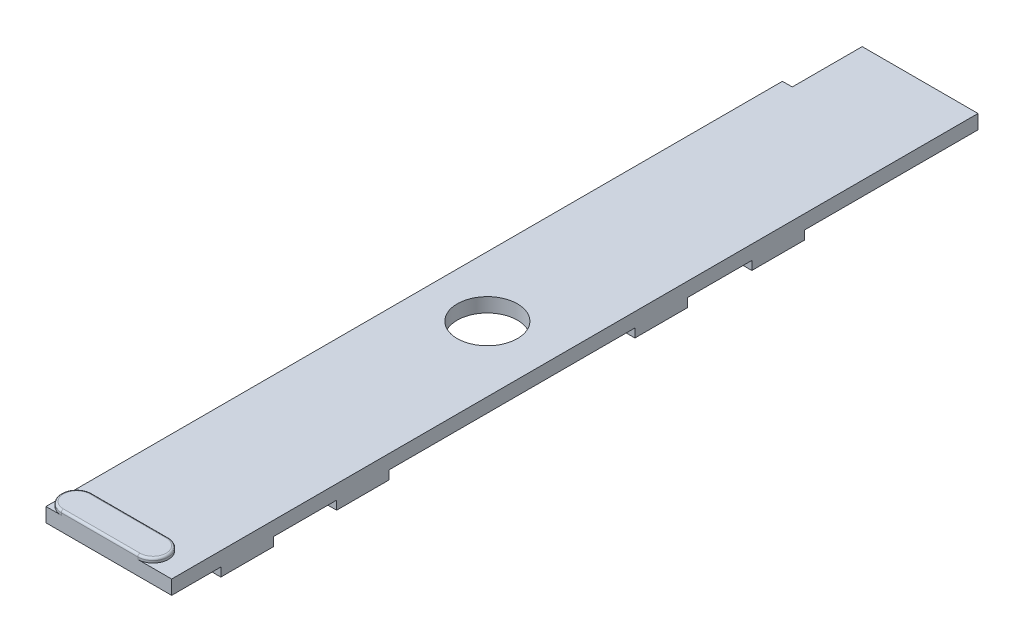
SolidWorks part; units mm, degrees
ref_plane "Front Plane" through (0, 0, 0) normal (0, 0, 1) x (1, 0, 0)
ref_plane "Top Plane" through (0, 0, 0) normal (0, 1, 0) x (1, 0, 0)
ref_plane "Right Plane" through (0, 0, 0) normal (1, 0, 0) x (0, 0, -1)
sketch "Sketch1" plane through (0, 0, 0) normal (0, 1, 0) x (1, 0, 0)
  line L1 (0, 0) -> (14.605, 0)
  line L2 (0, 0) -> (0, 93.726)
  line L3 (0, 93.726) -> (14.605, 93.726)
  line L4 (14.605, 0) -> (14.605, 93.726)
  line L5 (0, 93.726) -> (1.143, 93.726)
  line L6 (0, 93.726) -> (0, 85.598)
  line L7 (0, 85.598) -> (1.143, 85.598)
  line L8 (1.143, 93.726) -> (1.143, 85.598)
  circle A0 centre (7, 44.3) radius 3.5
  dimension "D1" = 14.605
  dimension "D5" = 7
  dimension "D2" = 93.726
  dimension "D3" = 8.128
  dimension "D4" = 1.143
  dimension "D6" = 7
  dimension "D7" = 44.3
extrude "Boss-Extrude1" add sketch "Sketch1" along normal blind 1.651 contours L3 L8 L7 L2 L1 L4 A0
sketch "Sketch2" plane through (0, 1.651, 0) normal (0, 1, 0) x (1, 0, 0)
  line L0 (1.778, 1.778) -> (10.668, 1.778) construction
  line L1 (1.778, 3.556) -> (10.668, 3.556)
  line L2 (1.778, 0) -> (10.668, 0)
  line L10 (14.605, 93.726) -> (1.143, 93.726)
  line L11 (1.143, 93.726) -> (1.143, 85.598)
  line L12 (1.143, 85.598) -> (0, 85.598)
  line L13 (0, 85.598) -> (0, 0)
  line L14 (0, 0) -> (14.605, 0)
  line L15 (14.605, 0) -> (14.605, 93.726)
  line L16 (14.605, 93.726) -> (1.143, 93.726)
  line L17 (1.143, 93.726) -> (1.143, 85.598)
  line L18 (1.143, 85.598) -> (0, 85.598)
  line L19 (0, 85.598) -> (0, 0)
  line L20 (0, 0) -> (14.605, 0)
  line L21 (14.605, 0) -> (14.605, 93.726)
  arc A0 (1.778, 3.556) -> (1.778, 0) centre (1.778, 1.778) ccw
  arc A1 (10.668, 0) -> (10.668, 3.556) centre (10.668, 1.778) ccw
  point P2 (6.223, 1.778)
  point P7 (12.446, 1.778)
  point P8 (0, 1.778)
  dimension "D1" = 1.778
  dimension "D2" = 12.446
  dimension "D3" = 0
extrude "Boss-Extrude2" add sketch "Sketch2" along normal blind 0.508
fillet "Fillet1" radius 0.254 4 edges at (6.223, 2.159, 0) (6.223, 2.159, -3.556) (0, 2.159, -1.778) (12.446, 2.159, -1.778)
sketch "Sketch3" plane through (0, 0, 0) normal (0, -1, 0) x (1, 0, 0)
  line L0 (14.605, 0) -> (14.605, -93.726) construction
  line L1 (14.605, -5.715) -> (9.906, -5.715)
  line L2 (14.605, -5.715) -> (14.605, -11.811)
  line L3 (14.605, -11.811) -> (9.906, -11.811)
  line L4 (9.906, -5.715) -> (9.906, -11.811)
  line L5 (0, 0) -> (0, -85.598) construction
  line L6 (14.605, -19.177) -> (9.906, -19.177)
  line L7 (14.605, -19.177) -> (14.605, -25.273)
  line L8 (14.605, -25.273) -> (9.906, -25.273)
  line L9 (9.906, -19.177) -> (9.906, -25.273)
  line L10 (14.605, -53.848) -> (9.906, -53.848)
  line L11 (14.605, -53.848) -> (14.605, -59.944)
  line L12 (14.605, -59.944) -> (9.906, -59.944)
  line L13 (9.906, -53.848) -> (9.906, -59.944)
  line L14 (14.605, -67.437) -> (9.906, -67.437)
  line L15 (14.605, -67.437) -> (14.605, -73.533)
  line L16 (14.605, -73.533) -> (9.906, -73.533)
  line L17 (9.906, -67.437) -> (9.906, -73.533)
  line L18 (0, -78.994) -> (4.699, -78.994)
  line L19 (0, -78.994) -> (0, -72.898)
  line L20 (0, -72.898) -> (4.699, -72.898)
  line L21 (4.699, -78.994) -> (4.699, -72.898)
  line L22 (0, -65.405) -> (4.699, -65.405)
  line L23 (0, -65.405) -> (0, -59.309)
  line L24 (0, -59.309) -> (4.699, -59.309)
  line L25 (4.699, -65.405) -> (4.699, -59.309)
  line L26 (0, 0) -> (14.605, 0) construction
  line L27 (0, -30.734) -> (4.699, -30.734)
  line L28 (0, -30.734) -> (0, -24.638)
  line L29 (0, -24.638) -> (4.699, -24.638)
  line L30 (4.699, -30.734) -> (4.699, -24.638)
  line L31 (0, -17.272) -> (4.699, -17.272)
  line L32 (0, -17.272) -> (0, -11.176)
  line L33 (0, -11.176) -> (4.699, -11.176)
  line L34 (4.699, -17.272) -> (4.699, -11.176)
  point P40 (12.2555, -59.944)
  dimension "D1" = 11.811
  dimension "D2" = 4.699
  dimension "D3" = 25.273
  dimension "D4" = 6.096
  dimension "D5" = 30.734
  dimension "D6" = 17.272
  dimension "D7" = 59.944
  dimension "D8" = 73.533
  dimension "D9" = 65.405
  dimension "D10" = 78.994
extrude "Boss-Extrude3" add sketch "Sketch3" along normal blind 1.016
